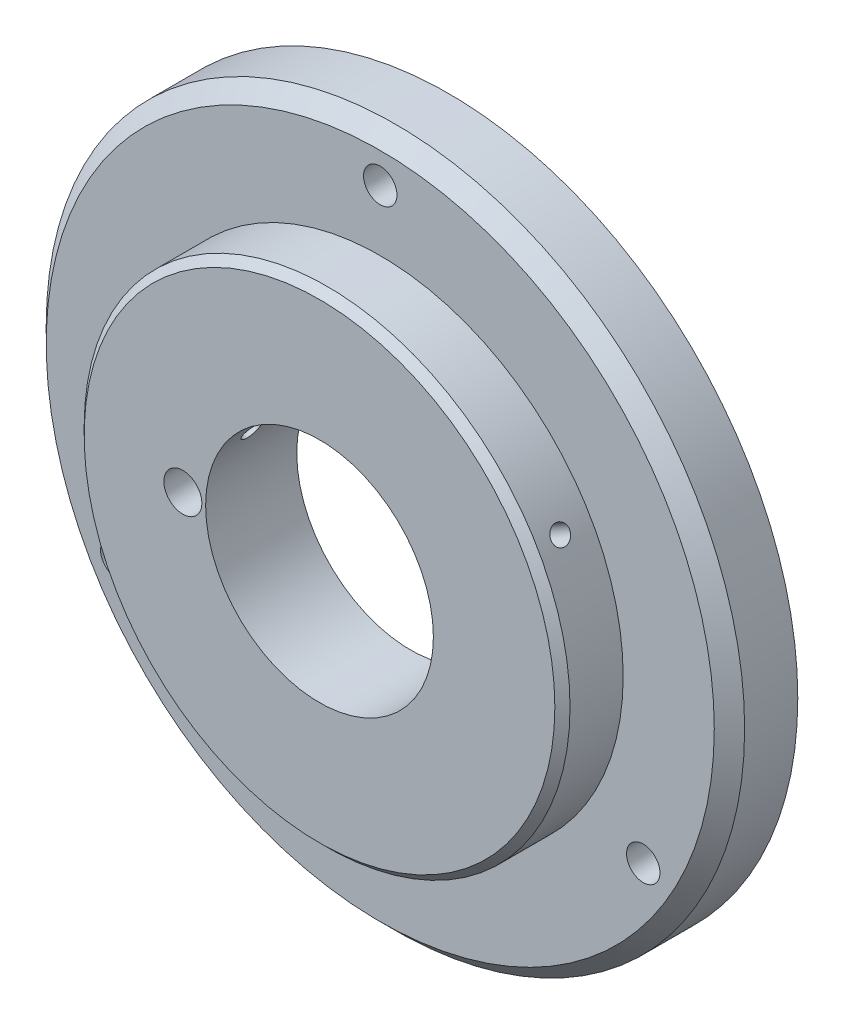
SolidWorks part; units mm, degrees
ref_plane "Plan1" through (0, 0, 0) normal (0, 0, 1) x (1, 0, 0)
ref_plane "Plan2" through (0, 0, 0) normal (0, 1, 0) x (1, 0, 0)
ref_plane "Plan3" through (0, 0, 0) normal (1, 0, 0) x (0, 0, -1)
sketch "Esquisse1" plane through (0, 0, 0) normal (0, 0, 1) x (1, 0, 0)
  circle A0 centre (0, 0) radius 46
  dimension "D1" = 92
extrude "Base-Extrusion" add sketch "Esquisse1" along normal blind 9
sketch "Esquisse2" plane through (0, 0, 9) normal (0, 0, 1) x (1, 0, 0)
  circle A0 centre (0, 0) radius 32
  dimension "D1" = 64
extrude "Boss.-Extru.1" add sketch "Esquisse2" along normal blind 8
sketch "Esquisse3" plane through (0, 0, 0) normal (0, 0, -1) x (-1, 0, 0)
  circle A0 centre (0, 0) radius 26
  dimension "D1" = 52
extrude "Enlèv. mat.-Extru.1" cut sketch "Esquisse3" against normal blind 5
sketch "Esquisse4" plane through (0, 0, 5) normal (0, 0, -1) x (-1, 0, 0)
  circle A0 centre (0, 0) radius 15
  dimension "D1" = 30
extrude "Enlèv. mat.-Extru.2" cut sketch "Esquisse4" against normal through all
sketch "Esquisse5" plane through (0, 0, 9) normal (0, 0, 1) x (1, 0, 0)
  line L0 (0, 0) -> (0, 40) construction
  circle A0 centre (0, 40) radius 2.2
  dimension "D2" = 4.4
  dimension "D1" = 40
extrude "Enlèv. mat.-Extru.3" cut sketch "Esquisse5" against normal through all
pattern_circular "Répétition circulaire1" count 3 every 120 about axis through (0, 0, 0) along (0, 0, 1) of "Enlèv. mat.-Extru.3"
chamfer "Chanfrein1" distance 2 angle 45 1 edges at (46, 0, 9)
chamfer "Chanfrein2" distance 1 angle 45 1 edges at (32, 0, 17)
ref_plane "Plan4" through (0, 0, 0) normal (0.866, 0.5, 0) x (0, 0, -1)
ref_plane "Plan5" through (27.7128, 16, 0) normal (0.866, 0.5, 0) x (0, 0, -1)
sketch "Esquisse8" plane through (27.7128, 16, 0) normal (0.866, 0.5, 0) x (0, 0, -1)
  line L0 (-7, 0) -> (0, 0) construction
  line L1 (-9, 44) -> (-9, -44) construction
  circle A0 centre (-13, 0) radius 1.225
  dimension "D1" = 2.45
  dimension "D2" = 4
extrude "Enlèv. mat.-Extru.4" cut sketch "Esquisse8" against normal up to next
cosmetic thread "Représentation de filetage2" parameters "D2"=3
pattern_circular "Répétition circulaire2" count 2 every 120 about axis through (0, 0, 17) along (0, 0, -1) of "Enlèv. mat.-Extru.4"
sketch "Esquisse9" plane through (0, 0, 17) normal (0, 0, 1) x (1, 0, 0)
  line L0 (-18, 0) -> (0, 0) construction
  circle A0 centre (-18, 0) radius 2.5
  dimension "D2" = 5
  dimension "D1" = 18
extrude "Enlèv. mat.-Extru.5" cut sketch "Esquisse9" against normal through all
equation "\"D1@Plan5\" = \"D1@Esquisse2\"/2"
